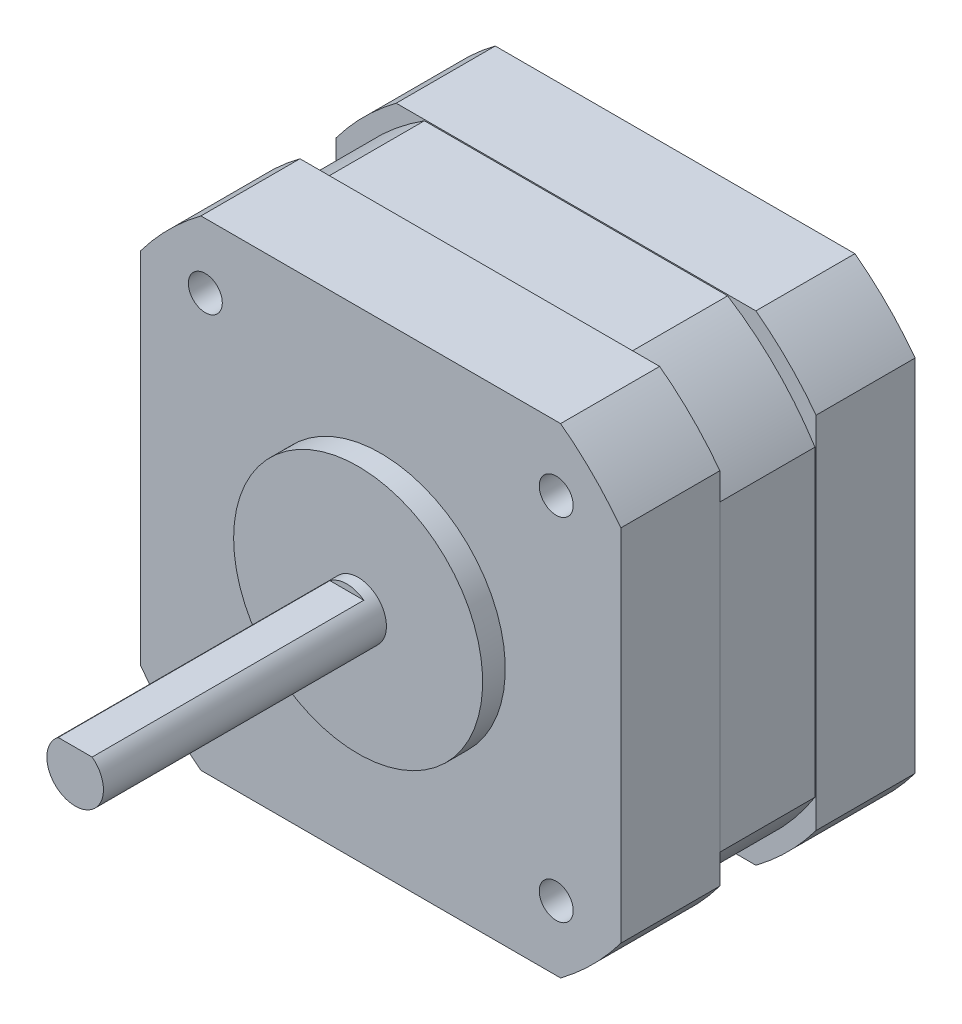
SolidWorks part; units mm, degrees
material "Plain Carbon Steel"
ref_plane "Front" through (0, 0, 0) normal (0, 0, 1) x (1, 0, 0)
ref_plane "Top" through (0, 0, 0) normal (0, 1, 0) x (1, 0, 0)
ref_plane "Right" through (0, 0, 0) normal (1, 0, 0) x (0, 0, -1)
sketch "Sketch1" plane through (0, 0, 0) normal (0, 0, 1) x (1, 0, 0)
  circle A0 centre (0, 0) radius 2.5
  dimension "D1" = 5
extrude "Boss-Extrude1" add sketch "Sketch1" along normal blind 27
sketch "Sketch2" plane through (0, 0, 0) normal (0, 0, -1) x (-1, 0, 0)
  circle A0 centre (0, 0) radius 11
  dimension "D1" = 22
extrude "Boss-Extrude2" add sketch "Sketch2" against normal blind 2
sketch "Sketch3" plane through (0, 0, 0) normal (0, 0, -1) x (-1, 0, 0)
  line L1 (21.209, -21.209) -> (-21.209, -21.209)
  line L2 (21.209, -21.209) -> (21.209, 21.209)
  line L3 (21.209, 21.209) -> (-21.209, 21.209)
  line L4 (-21.209, -21.209) -> (-21.209, 21.209)
  line L5 (21.209, -21.209) -> (-21.209, 21.209) construction
  line L6 (21.209, 21.209) -> (-21.209, -21.209) construction
  point P0 (0, 0)
  dimension "D1" = 42.418
extrude "Boss-Extrude3" add sketch "Sketch3" along normal blind 26
sketch "Sketch4" plane through (0, 0, -26) normal (0, 0, -1) x (-1, 0, 0)
  line L0 (-21.209, -15.888) -> (-21.209, -21.209)
  line L1 (15.888, -21.209) -> (21.209, -21.209)
  line L2 (21.209, 15.888) -> (21.209, 21.209)
  line L3 (-15.888, 21.209) -> (-21.209, 21.209)
  line L4 (-21.209, 21.209) -> (-21.209, -21.209)
  line L5 (-21.209, -21.209) -> (21.209, -21.209)
  line L6 (21.209, -21.209) -> (21.209, 21.209)
  line L7 (21.209, 21.209) -> (-21.209, 21.209)
  line L8 (-21.209, 21.209) -> (-21.209, 15.888)
  line L9 (-21.209, -21.209) -> (-15.888, -21.209)
  line L10 (21.209, -21.209) -> (21.209, -15.888)
  line L11 (21.209, 21.209) -> (15.888, 21.209)
  arc A0 (-21.209, -15.888) -> (-15.888, -21.209) centre (0, 0) ccw
  arc A1 (15.888, -21.209) -> (21.209, -15.888) centre (0, 0) ccw
  arc A2 (21.209, 15.888) -> (15.888, 21.209) centre (0, 0) ccw
  arc A3 (-15.888, 21.209) -> (-21.209, 15.888) centre (0, 0) ccw
  dimension "D2" = 26.5
  dimension "D1" = 0
extrude "Cut-Extrude1" cut sketch "Sketch4" against normal through all
hole_wizard "M3x0.5 Tapped Hole1" positions "Sketch6" profile "Sketch5" tap size "M3x0.5" standard "ANSI Metric"
sketch "Sketch6" plane through (0, 0, 0) normal (0, 0, 1) x (1, 0, 0)
  line L0 (-16.1632, 0) -> (0, 0) construction
  line L1 (0, 0) -> (0, 15.0764) construction
  point P0 (-15.5, 15.5)
  point P11 (-15.5, -15.5)
  point P12 (15.5, -15.5)
  point P13 (15.5, 15.5)
  dimension "D1" = 31
  dimension "D2" = 31
sketch "Sketch5" plane through (-15.5, 15.5, 0) normal (1, 0, 0) x (0, -1, 0)
  line L0 (0, 0) -> (0, 8.2511)
  line L1 (0, 8.2511) -> (1.25, 7.5)
  line L2 (1.25, 7.5) -> (1.25, 6)
  line L3 (1.25, 6) -> (1.5, 6)
  line L4 (1.5, 6) -> (1.5, 0)
  line L5 (1.5, 0) -> (0, 0)
  line L10 (0, 8.2511) -> (-1.25, 7.5) construction
  line L11 (0, -6.35) -> (0, 107.95) construction
  dimension "Tap Drill Dia." = 2.5
  dimension "Tap Drill Depth" = 7.5
  dimension "Thread Major Dia." = 3
  dimension "Thread Depth" = 6
  dimension "Drill Angle" = 118
sketch "Sketch7" plane through (0, 0, 27) normal (0, 0, 1) x (1, 0, 0)
  line L0 (-1.5, 2) -> (1.5, 2)
  circle A0 centre (0, 0) radius 2.5 construction
  circle A1 centre (0, 0) radius 2.5 construction
  arc A2 (1.5, 2) -> (-1.5, 2) centre (0, 0) ccw
  dimension "D1" = 4.5
extrude "Cut-Extrude2" cut sketch "Sketch7" against normal blind 24
ref_plane "Plane1" through (0, 0, -13) normal (0, 0, 1) x (1, 0, 0)
sketch "Sketch8" plane through (0, 0, -13) normal (0, 0, 1) x (1, 0, 0)
  line L0 (-13.3944, 21.109) -> (13.3944, 21.109)
  line L1 (-5.7152, 0) -> (0, 0) construction
  line L2 (0, 0) -> (0, 8.4579) construction
  line L3 (-15.888, 21.209) -> (15.888, 21.209) construction
  line L4 (-13.3944, -21.109) -> (13.3944, -21.109)
  line L5 (-21.109, 13.3944) -> (-21.109, -13.3944)
  line L6 (-21.209, -15.888) -> (-21.209, 15.888) construction
  line L7 (21.109, 13.3944) -> (21.109, -13.3944)
  line L12 (15.888, 21.209) -> (-15.888, 21.209)
  line L13 (-21.209, 15.888) -> (-21.209, -15.888)
  line L14 (-15.888, -21.209) -> (15.888, -21.209)
  line L15 (21.209, -15.888) -> (21.209, 15.888)
  line L16 (15.888, 21.209) -> (-15.888, 21.209)
  line L17 (-21.209, 15.888) -> (-21.209, -15.888)
  line L18 (-15.888, -21.209) -> (15.888, -21.209)
  line L19 (21.209, -15.888) -> (21.209, 15.888)
  arc A0 (-13.3944, 21.109) -> (-21.109, 13.3944) centre (0, 0) ccw
  arc A1 (-21.109, -13.3944) -> (-13.3944, -21.109) centre (0, 0) ccw
  arc A2 (21.109, 13.3944) -> (13.3944, 21.109) centre (0, 0) ccw
  arc A3 (13.3944, -21.109) -> (21.109, -13.3944) centre (0, 0) ccw
  arc A5 (-15.888, 21.209) -> (-21.209, 15.888) centre (0, 0) ccw
  arc A6 (-21.209, -15.888) -> (-15.888, -21.209) centre (0, 0) ccw
  arc A7 (15.888, -21.209) -> (21.209, -15.888) centre (0, 0) ccw
  arc A8 (21.209, 15.888) -> (15.888, 21.209) centre (0, 0) ccw
  arc A9 (-15.888, 21.209) -> (-21.209, 15.888) centre (0, 0) ccw
  arc A10 (-21.209, -15.888) -> (-15.888, -21.209) centre (0, 0) ccw
  arc A11 (15.888, -21.209) -> (21.209, -15.888) centre (0, 0) ccw
  arc A12 (21.209, 15.888) -> (15.888, 21.209) centre (0, 0) ccw
  dimension "D1" = 50
  dimension "D2" = 0.1
  dimension "D3" = 0.1
  dimension "D4" = 0
extrude "Cut-Extrude3" cut sketch "Sketch8" against normal offset from surface 8.75 and the other way offset from surface (4.25 mm away) 8.75 up to face at (0, 0, -26) other way up to face at (-14, 15.5, 0)
